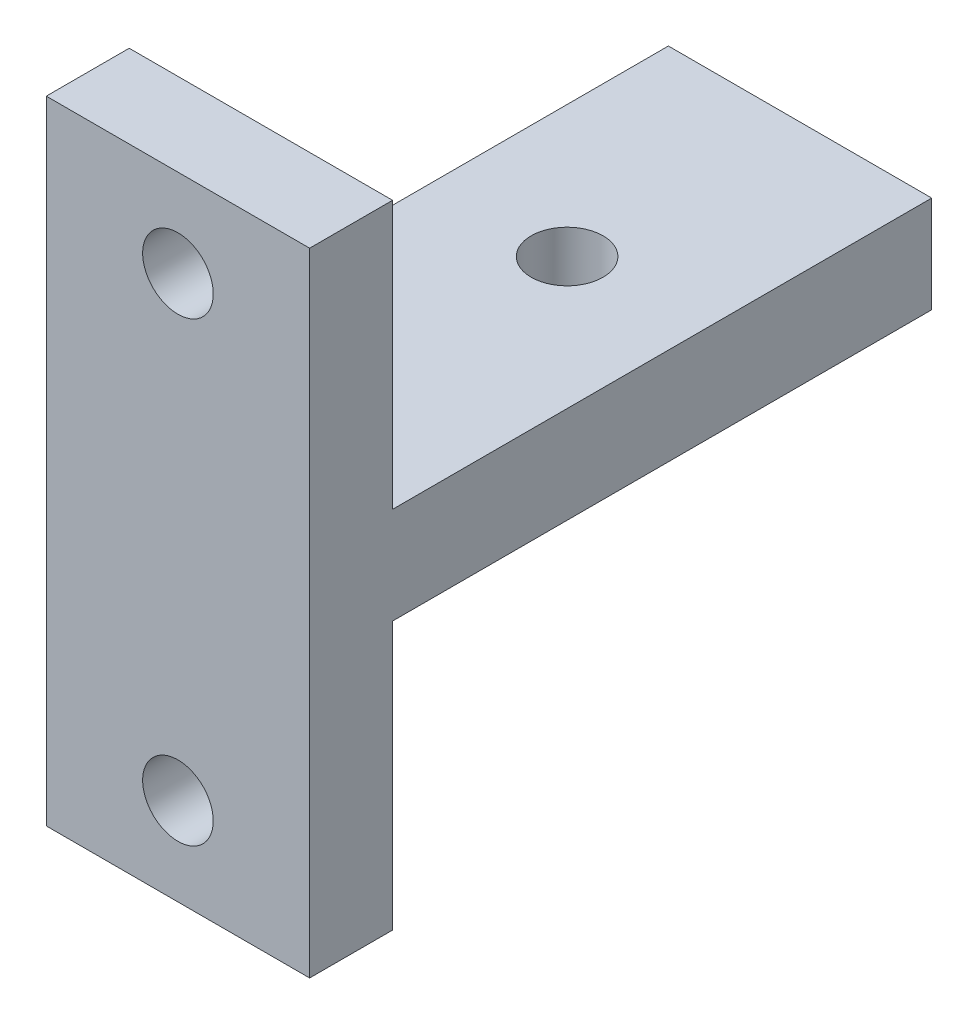
SolidWorks part; units mm, degrees
ref_plane "Front Plane" through (0, 0, 0) normal (0, 0, 1) x (1, 0, 0)
ref_plane "Top Plane" through (0, 0, 0) normal (0, 1, 0) x (1, 0, 0)
ref_plane "Right Plane" through (0, 0, 0) normal (1, 0, 0) x (0, 0, -1)
sketch "Sketch1" plane through (0, 0, 0) normal (0, 0, 1) x (1, 0, 0)
  line L0 (-9.525, 0) -> (9.525, 0) construction
  line L1 (-9.525, -22.86) -> (9.525, -22.86)
  line L2 (-9.525, -22.86) -> (-9.525, 22.86)
  line L3 (-9.525, 22.86) -> (9.525, 22.86)
  line L4 (9.525, -22.86) -> (9.525, 22.86)
  line L5 (-9.525, -22.86) -> (9.525, 22.86) construction
  line L6 (-9.525, 22.86) -> (9.525, -22.86) construction
  line L7 (-9.525, -3.5) -> (9.525, -3.5)
  line L8 (-9.525, -3.5) -> (-9.525, 3.5)
  line L9 (-9.525, 3.5) -> (9.525, 3.5)
  line L10 (9.525, -3.5) -> (9.525, 3.5)
  line L11 (-9.525, -3.5) -> (9.525, 3.5) construction
  line L12 (-9.525, 3.5) -> (9.525, -3.5) construction
  line L13 (0, 22.86) -> (0, -22.86) construction
  circle A0 centre (0, 16.51) radius 2.5527
  circle A1 centre (0, -16.51) radius 2.5527
  point P0 (0, 0)
  point P6 (0, 0)
  dimension "D4" = 5.1054
  dimension "D1" = 45.72
  dimension "D2" = 19.05
  dimension "D3" = 7
  dimension "D5" = 33.02
extrude "Boss-Extrude1" add sketch "Sketch1" against normal blind 6 contours L2 L9 L4 L3 A0 | L7 L2 L1 L4 A1 | L9 L2 L7 L4
sketch "Sketch3" plane through (0, 0, 0) normal (0, 0, 1) x (1, 0, 0)
  line L1 (-9.525, -3.5) -> (9.525, -3.5)
  line L2 (-9.525, -3.5) -> (-9.525, 3.5)
  line L3 (-9.525, 3.5) -> (9.525, 3.5)
  line L4 (9.525, -3.5) -> (9.525, 3.5)
  line L5 (-9.525, -3.5) -> (9.525, 3.5) construction
  line L6 (-9.525, 3.5) -> (9.525, -3.5) construction
  point P0 (0, 0)
extrude "Boss-Extrude2" add sketch "Sketch3" against normal blind 45
sketch "Sketch4" plane through (0, 3.5, 0) normal (0, 1, 0) x (1, 0, 0)
  line L0 (0, 45) -> (0, 0) construction
  line L1 (9.525, 45) -> (-9.525, 45) construction
  line L2 (-9.525, 0) -> (9.525, 0) construction
  circle A0 centre (0, 28.15) radius 2.6
  dimension "D1" = 5.2
  dimension "D2" = 28.15
extrude "Cut-Extrude1" cut sketch "Sketch4" against normal through all
